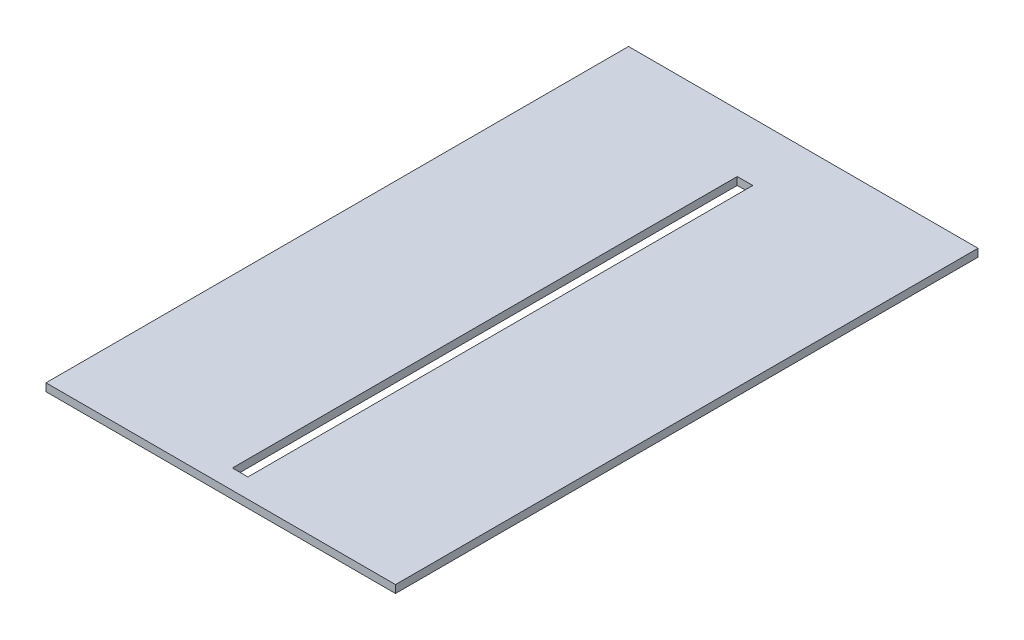
SolidWorks part; units mm, degrees
ref_plane "Спереди" through (0, 0, 0) normal (0, 0, 1) x (1, 0, 0)
ref_plane "Сверху" through (0, 0, 0) normal (0, 1, 0) x (1, 0, 0)
ref_plane "Справа" through (0, 0, 0) normal (1, 0, 0) x (0, 0, -1)
sketch "Эскиз1" plane through (0, 0, 0) normal (0, 1, 0) x (1, 0, 0)
  line L1 (-225, -375) -> (225, -375)
  line L2 (-225, -375) -> (-225, 375)
  line L3 (-225, 375) -> (225, 375)
  line L4 (225, -375) -> (225, 375)
  line L5 (-225, -375) -> (225, 375) construction
  line L6 (-225, 375) -> (225, -375) construction
  line L7 (-10, 300) -> (10, 300)
  line L8 (-10, 300) -> (-10, -350)
  line L9 (-10, -350) -> (10, -350)
  line L10 (10, 300) -> (10, -350)
  point P0 (0, 0)
  point P10 (0, 0)
  point P11 (0, 0)
  point P12 (0, 0)
  point P13 (0, 0)
  point P14 (0, 0)
  point P15 (0, 0)
extrude "Бобышка-Вытянуть1" add sketch "Эскиз1" along normal blind 10
